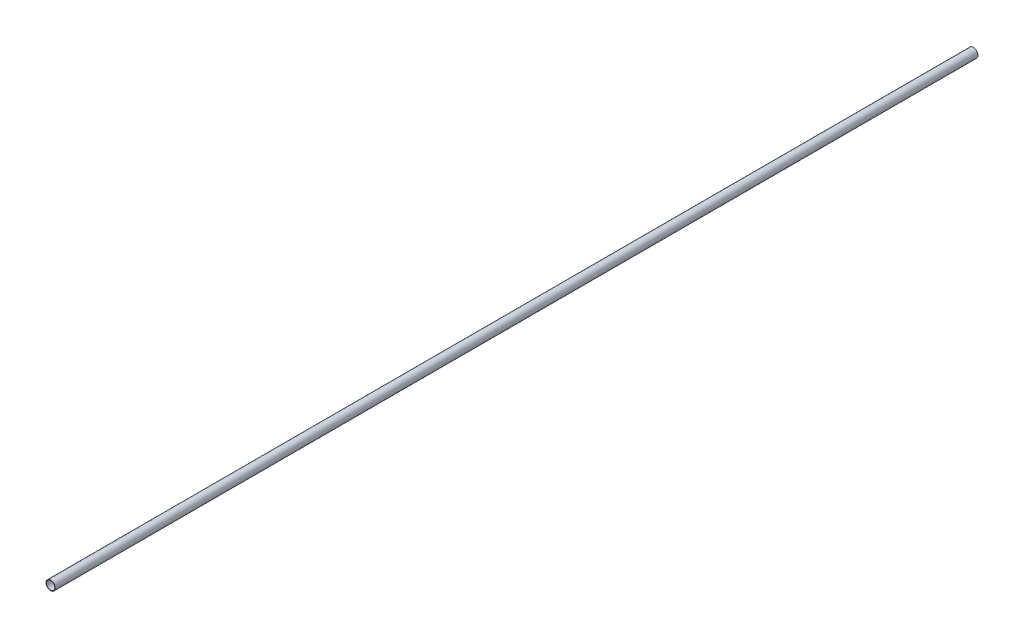
SolidWorks part; units mm, degrees
material "carbon fiber"
ref_plane "Front Plane" through (0, 0, 0) normal (0, 0, 1) x (1, 0, 0)
ref_plane "Top Plane" through (0, 0, 0) normal (0, 1, 0) x (1, 0, 0)
ref_plane "Right Plane" through (0, 0, 0) normal (1, 0, 0) x (0, 0, -1)
sketch "Эскиз1" plane through (0, 0, 0) normal (0, 0, 1) x (1, 0, 0)
  circle A0 centre (0, 0) radius 5
  circle A1 centre (0, 0) radius 4.5
  dimension "D1" = 10
  dimension "D2" = 0.5
extrude "Бобышка-Вытянуть1" add sketch "Эскиз1" along normal mid plane 1000
